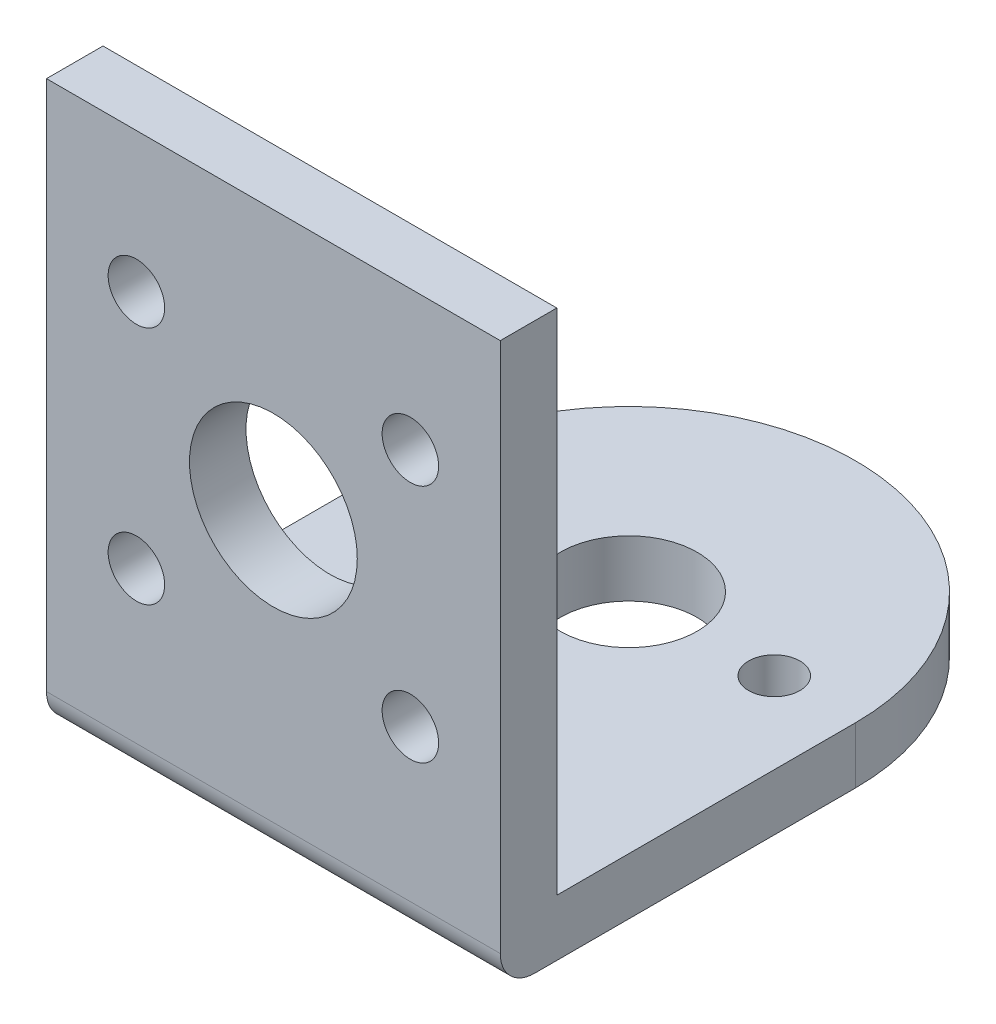
SolidWorks part; units mm, degrees
ref_plane "Front Plane" through (0, 0, 0) normal (0, 0, 1) x (1, 0, 0)
ref_plane "Top Plane" through (0, 0, 0) normal (0, 1, 0) x (1, 0, 0)
ref_plane "Right Plane" through (0, 0, 0) normal (1, 0, 0) x (0, 0, -1)
other "Configuration Table"
sketch "Base Face" plane through (0, 0, 0) normal (0, 1, 0) x (1, 0, 0)
  line L2 (-13.25, 0) -> (-13.25, -20.75)
  line L3 (-13.25, -20.75) -> (13.25, -20.75)
  line L4 (13.25, 0) -> (13.25, -20.75)
  line L5 (-13.25, -20.75) -> (13.25, -20.75)
  line L6 (-13.25, -20.75) -> (-13.25, -17.45)
  line L7 (-13.25, -17.45) -> (13.25, -17.45)
  line L8 (13.25, -20.75) -> (13.25, -17.45)
  arc A0 (13.25, 0) -> (-13.25, 0) centre (0, 0) ccw
  circle A1 centre (0, 0) radius 4
  circle A2 centre (-8.5, 0) radius 1.5
  circle A3 centre (8.5, 0) radius 1.5
  dimension "D1" = 26.5
  dimension "D2" = 8
  dimension "D3" = 3
  dimension "D4" = 3
  dimension "D6" = 3.3
  dimension "D7" = 0
  dimension "D8" = 8.5
  dimension "D10" = 34
  dimension "D5" = 20.75
  dimension "D9" = 17
extrude "Base" add sketch "Base Face" along normal blind 3.3 contours A2 | A1 | A3 | L3 L4 A0 L2
sketch "Top sketch" plane through (0, 0, 20.75) normal (0, 0, 1) x (1, 0, 0)
  line L1 (-13.25, 0) -> (13.25, 0)
  line L2 (-13.25, 0) -> (-13.25, 33)
  line L3 (-13.25, 33) -> (13.25, 33)
  line L4 (13.25, 0) -> (13.25, 33)
  circle A5 centre (0, 17.8) radius 4.9
  circle A6 centre (8, 10.85) radius 1.65
  circle A7 centre (8, 24.85) radius 1.65
  circle A8 centre (-8, 10.85) radius 1.65
  circle A9 centre (-8, 24.85) radius 1.65
  dimension "D1" = 15.2
  dimension "D3" = 14
  dimension "D2" = 8.15
  dimension "D4" = 3.3
  dimension "D7" = 9.8
  dimension "D5" = 16
  dimension "D6" = 26.5
  dimension "D8" = 13.25
  dimension "D9" = 33
  dimension "D10" = 5.25
sketch "Sketch3" plane through (0, 0, 20.75) normal (0, 0, 1) x (1, 0, 0)
  line L0 (-13.25, 0) -> (13.25, 0)
  line L1 (-13.25, 0) -> (-13.25, 33)
  line L2 (-13.25, 33) -> (13.25, 33)
  line L3 (13.25, 0) -> (13.25, 33)
  circle A0 centre (0, 17.8) radius 4.9
  circle A1 centre (8, 10.85) radius 1.65
  circle A2 centre (8, 24.85) radius 1.65
  circle A3 centre (-8, 10.85) radius 1.65
  circle A4 centre (-8, 24.85) radius 1.65
  dimension "D2" = 10.5973
  dimension "D1" = 14
extrude "Boss-Extrude2" add sketch "Sketch3" against normal blind 3.3
fillet "Fillet1" radius 2 1 edges at (0, 0, 20.75)
sketch "Sketch4" plane through (0, 0, 17.45) normal (0, 0, -1) x (-1, 0, 0)
  line L0 (-13.25, 3.3) -> (-13.25, 0) construction
  line L1 (-13.25, 0) -> (13.25, 0) construction
  line L2 (13.25, 3.3) -> (13.25, 0) construction
  line L3 (-13.25, 3.3) -> (-13.25, 0)
  line L4 (-13.25, 33) -> (-13.25, 3.3)
  line L5 (-13.25, 3.3) -> (13.25, 3.3)
  line L6 (13.25, 3.3) -> (13.25, 33)
  line L7 (13.25, 33) -> (-13.25, 33)
  line L8 (-13.25, 33) -> (-13.25, 3.3)
  line L9 (-13.25, 3.3) -> (13.25, 3.3)
  line L10 (13.25, 3.3) -> (13.25, 33)
  line L11 (13.25, 33) -> (-13.25, 33)
  line L12 (-13.25, 0) -> (13.25, 0)
  line L13 (13.25, 3.3) -> (13.25, 0)
  line L14 (0, 17.8) -> (0, 24.85)
  line L15 (0, 17.8) -> (8, 17.8)
  line L16 (0, 17.8) -> (0, 10.85)
  circle A0 centre (8, 10.85) radius 1.65 construction
  circle A1 centre (8, 24.85) radius 1.65 construction
  circle A2 centre (-8, 24.85) radius 1.65 construction
  circle A3 centre (0, 17.8) radius 4.9 construction
  circle A4 centre (-8, 10.85) radius 1.65 construction
  circle A5 centre (8, 10.85) radius 1.65
  circle A6 centre (8, 24.85) radius 1.65
  circle A7 centre (-8, 24.85) radius 1.65
  circle A8 centre (0, 17.8) radius 4.9
  circle A9 centre (-8, 10.85) radius 1.65
  dimension "D2" = 17.8
  dimension "D4" = 8
  dimension "D3" = 7.05
  dimension "D1" = 0
